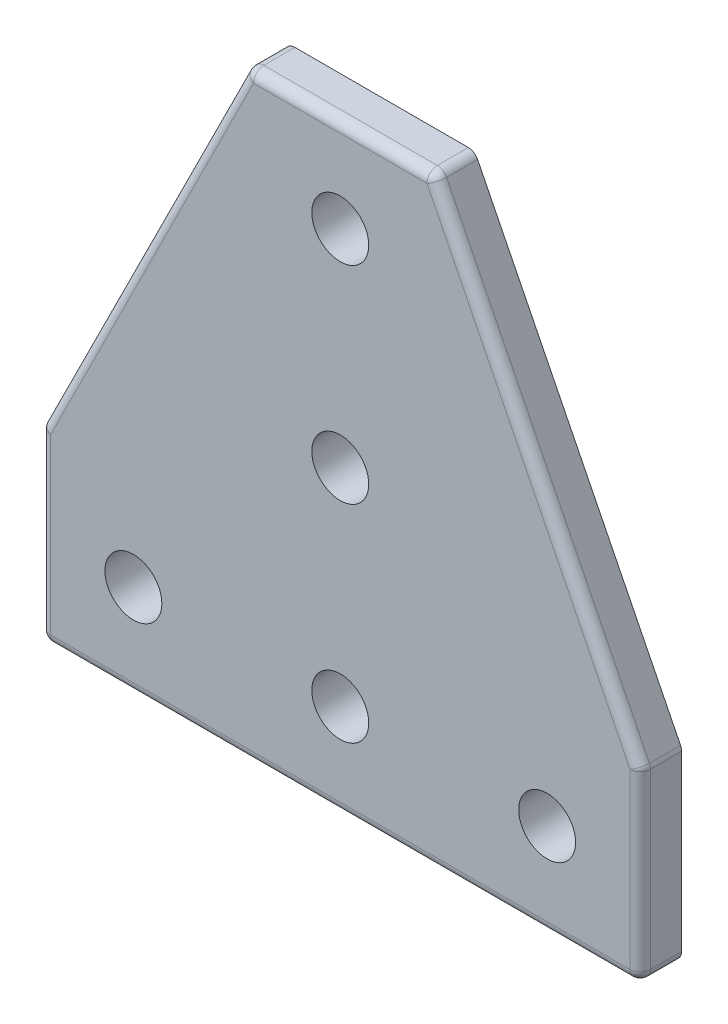
SolidWorks part; units mm, degrees
material "6061-T6 (SS)"
ref_plane "Front Plane" through (0, 0, 0) normal (0, 0, 1) x (1, 0, 0)
ref_plane "Top Plane" through (0, 0, 0) normal (0, 1, 0) x (1, 0, 0)
ref_plane "Right Plane" through (0, 0, 0) normal (1, 0, 0) x (0, 0, -1)
sketch "Sketch1" plane through (0, 0, 0) normal (0, 0, 1) x (1, 0, 0)
  line L0 (0, 0) -> (0, 18)
  line L1 (9, 9) -> (29, 9) construction
  line L2 (29, 9) -> (49, 9) construction
  line L3 (29, 9) -> (29, 29) construction
  line L4 (38, 58) -> (20, 58)
  line L5 (58, 0) -> (0, 0)
  line L6 (29, 29) -> (29, 49) construction
  line L7 (58, 18) -> (58, 0)
  line L8 (38, 58) -> (58, 18)
  line L9 (58, 9) -> (49, 9) construction
  line L10 (29, 58) -> (29, 49) construction
  line L11 (0, 18) -> (20, 58)
  circle A0 centre (9, 9) radius 2.75
  circle A1 centre (29, 9) radius 2.75
  circle A2 centre (49, 9) radius 2.75
  circle A3 centre (29, 29) radius 2.75
  circle A4 centre (29, 49) radius 2.75
  dimension "D1" = 20
  dimension "E" = 5.5
  dimension "D2" = 9
  dimension "C" = 58
  dimension "D3" = 20
  dimension "B" = 58
  dimension "D4" = 9
  dimension "D5" = 18
extrude "Boss-Extrude1" add sketch "Sketch1" along normal mid plane 4
fillet "Fillet1" radius 1 12 edges at (0, 0, 0) (0, 9, 2) (29, 0, 2) (58, 9, 2) (58, 0, 0) (29, 58, 2) (48, 38, 2) (58, 18, 0) (38, 58, 0) (10, 38, 2) (20, 58, 0) (0, 18, 0)
